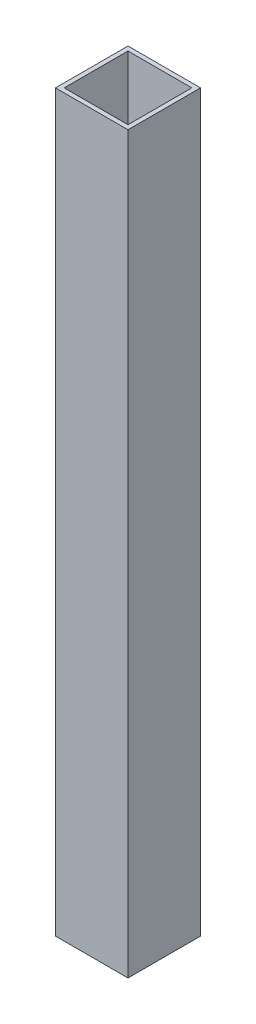
SolidWorks part; units mm, degrees
material "ASTM A36 Acero"
ref_plane "Alzado" through (0, 0, 0) normal (0, 0, 1) x (1, 0, 0)
ref_plane "Planta" through (0, 0, 0) normal (0, 1, 0) x (1, 0, 0)
ref_plane "Vista lateral" through (0, 0, 0) normal (1, 0, 0) x (0, 0, -1)
sketch "Croquis1" plane through (0, 0, 0) normal (0, 1, 0) x (1, 0, 0)
  line L0 (-27.8514, 32) -> (16.1486, 32)
  line L1 (-30.8514, -15) -> (19.1486, -15)
  line L2 (-30.8514, -15) -> (-30.8514, 35)
  line L3 (-30.8514, 35) -> (19.1486, 35)
  line L4 (19.1486, -15) -> (19.1486, 35)
  line L5 (-30.8514, -15) -> (19.1486, 35) construction
  line L6 (-30.8514, 35) -> (19.1486, -15) construction
  line L7 (16.1486, -12) -> (16.1486, 32)
  line L8 (-27.8514, -12) -> (16.1486, -12)
  line L9 (-27.8514, -12) -> (-27.8514, 32)
  dimension "D1" = 50
  dimension "D2" = 3
extrude "Saliente-Extruir1" add sketch "Croquis1" along normal blind 506.49
